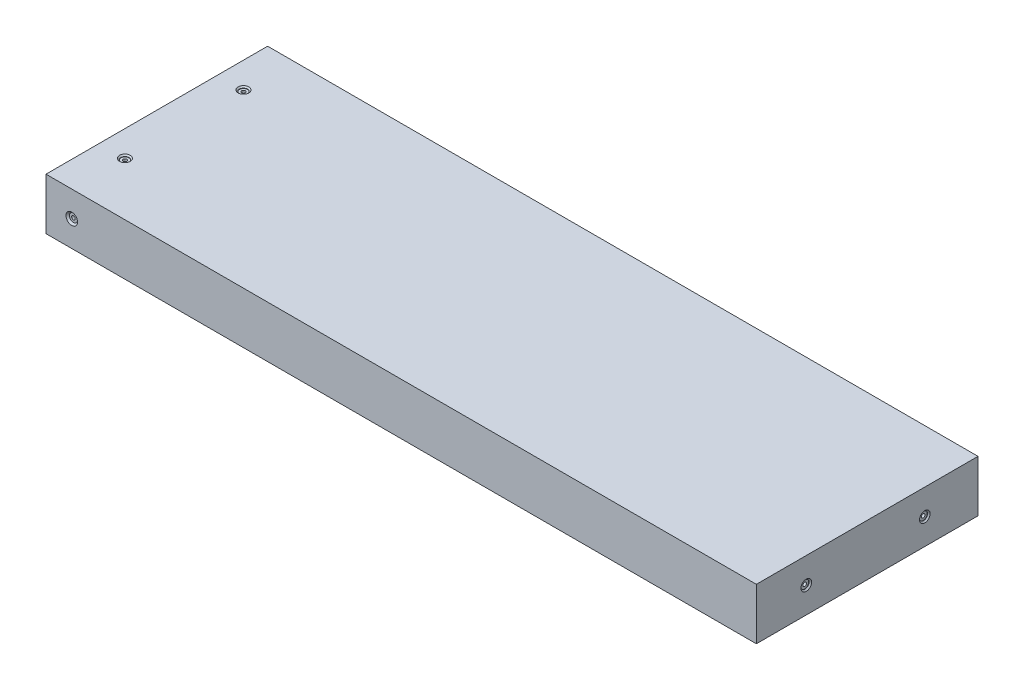
SolidWorks part; units mm, degrees
ref_plane "Front Plane" through (0, 0, 0) normal (0, 0, 1) x (1, 0, 0)
ref_plane "Top Plane" through (0, 0, 0) normal (0, 1, 0) x (1, 0, 0)
ref_plane "Right Plane" through (0, 0, 0) normal (1, 0, 0) x (0, 0, -1)
sketch "Sketch1" plane through (0, 0, 0) normal (0, 1, 0) x (1, 0, 0)
  line L1 (-175, 54.6) -> (175, 54.6)
  line L2 (-175, 54.6) -> (-175, -54.6)
  line L3 (-175, -54.6) -> (175, -54.6)
  line L4 (175, 54.6) -> (175, -54.6)
  line L5 (-175, 54.6) -> (175, -54.6) construction
  line L6 (-175, -54.6) -> (175, 54.6) construction
  point P0 (0, 0)
  dimension "D1" = 109.2
  dimension "D2" = 350
extrude "Boss-Extrude1" add sketch "Sketch1" along normal blind 25.4
hole_wizard "CBORE for #0 Binding Head Machine Screw1" positions "Sketch2" profile "Sketch3" counterbore size "#0" standard "ANSI Inch"
sketch "Sketch2" plane through (0, 0, 54.6) normal (0, 0, 1) x (1, 0, 0)
  line L0 (-175, 25.4) -> (-175, 0) construction
  line L1 (-175, 25.4) -> (175, 25.4) construction
  point P0 (-162.3, 12.7)
  dimension "D1" = 12.7
  dimension "D2" = 12.7
sketch "Sketch3" plane through (-162.3, 12.7, 54.6) normal (1, 0, 0) x (0, -1, 0)
  line L0 (0, 0) -> (0, 30.5342)
  line L1 (0, 30.5342) -> (0.889, 30)
  line L2 (0.889, 30) -> (0.889, 0.8128)
  line L3 (0.889, 0.8128) -> (1.985, 0.8128)
  line L5 (1.985, 0.8128) -> (1.985, 0.8725)
  line L6 (1.985, 0.8725) -> (2.8575, 0)
  line L7 (2.8575, 0) -> (0, 0)
  line L8 (-1.985, 0.8725) -> (-2.8575, 0) construction
  line L10 (0, 30.5342) -> (-0.889, 30) construction
  line L11 (0, -6.35) -> (0, 107.95) construction
  dimension "Hole Dia." = 1.778
  dimension "Hole Depth" = 30
  dimension "C'Bore Dia." = 3.97
  dimension "C'Bore Depth" = 0.8128
  dimension "Near C'Sink Dia." = 5.715
  dimension "Near C'Sink Angle" = 90
  dimension "Drill Angle" = 118
mirror "Mirror1" about plane through (0, 0, 0) normal (0, 0, 1) of "CBORE for #0 Binding Head Machine Screw1"
hole_wizard "CBORE for #0 Binding Head Machine Screw2" positions "Sketch4" profile "Sketch5" counterbore size "#0" standard "ANSI Inch"
sketch "Sketch4" plane through (175, 0, 0) normal (1, 0, 0) x (0, 0, -1)
  line L0 (-54.6, 25.4) -> (-54.6, 0) construction
  line L2 (-54.6, 25.4) -> (54.6, 25.4) construction
  point P0 (-30, 12.7)
  point P2 (28.4, 12.7)
  dimension "D1" = 58.4
  dimension "D2" = 24.6
  dimension "D4" = 12.7
sketch "Sketch5" plane through (175, 12.7, 30) normal (0, 1, 0) x (0, 0, -1)
  line L0 (0, 0) -> (0, 30.5342)
  line L1 (0, 30.5342) -> (0.889, 30)
  line L2 (0.889, 30) -> (0.889, 0.8128)
  line L3 (0.889, 0.8128) -> (1.985, 0.8128)
  line L5 (1.985, 0.8128) -> (1.985, 0.635)
  line L6 (1.985, 0.635) -> (2.62, 0)
  line L7 (2.62, 0) -> (0, 0)
  line L8 (-1.985, 0.635) -> (-2.62, 0) construction
  line L10 (0, 30.5342) -> (-0.889, 30) construction
  line L11 (0, -6.35) -> (0, 107.95) construction
  dimension "Hole Dia." = 1.778
  dimension "Hole Depth" = 30
  dimension "C'Bore Dia." = 3.97
  dimension "C'Bore Depth" = 0.8128
  dimension "Near C'Sink Dia." = 5.24
  dimension "Near C'Sink Angle" = 90
  dimension "Drill Angle" = 118
hole_wizard "CBORE for #0 Binding Head Machine Screw3" positions "Sketch6" profile "Sketch7" counterbore size "#0" standard "ANSI Inch"
sketch "Sketch6" plane through (0, 25.4, 0) normal (0, 1, 0) x (1, 0, 0)
  line L0 (-175, 54.6) -> (-175, -54.6) construction
  line L1 (175, 54.6) -> (-175, 54.6) construction
  point P0 (-162.3, 30)
  point P2 (-162.3, -28.4)
  dimension "D1" = 12.7
  dimension "D2" = 58.4
  dimension "D3" = 24.6
  dimension "D4" = 12.7
sketch "Sketch7" plane through (-162.3, 25.4, -30) normal (1, 0, 0) x (0, 0, 1)
  line L0 (0, 0) -> (0, 30.5342)
  line L1 (0, 30.5342) -> (0.889, 30)
  line L2 (0.889, 30) -> (0.889, 0.8128)
  line L3 (0.889, 0.8128) -> (1.985, 0.8128)
  line L5 (1.985, 0.8128) -> (1.985, 0.635)
  line L6 (1.985, 0.635) -> (2.62, 0)
  line L7 (2.62, 0) -> (0, 0)
  line L8 (-1.985, 0.635) -> (-2.62, 0) construction
  line L10 (0, 30.5342) -> (-0.889, 30) construction
  line L11 (0, -6.35) -> (0, 107.95) construction
  dimension "Hole Dia." = 1.778
  dimension "Hole Depth" = 30
  dimension "C'Bore Dia." = 3.97
  dimension "C'Bore Depth" = 0.8128
  dimension "Near C'Sink Dia." = 5.24
  dimension "Near C'Sink Angle" = 90
  dimension "Drill Angle" = 118
